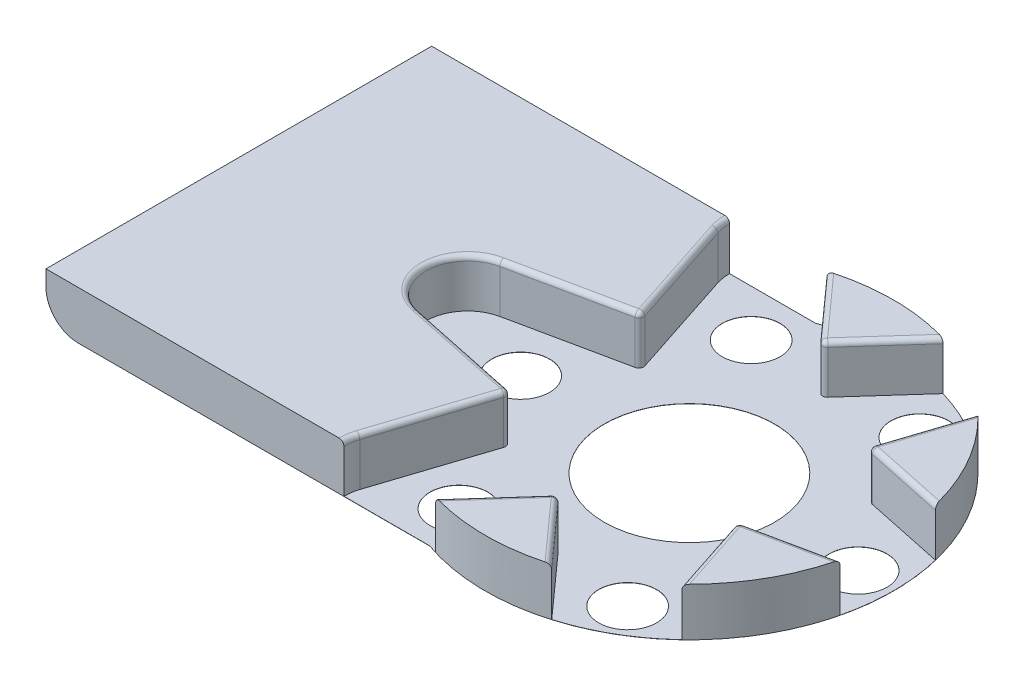
SolidWorks part; units mm, degrees
ref_plane "Alzado" through (0, 0, 0) normal (0, 0, 1) x (1, 0, 0)
ref_plane "Planta" through (0, 0, 0) normal (0, 1, 0) x (1, 0, 0)
ref_plane "Vista lateral" through (0, 0, 0) normal (1, 0, 0) x (0, 0, -1)
sketch "Croquis1" plane through (0, 0, 0) normal (0, 1, 0) x (1, 0, 0)
  line L0 (-28.04, 12) -> (-4.1581, 12)
  line L1 (-28.04, -12) -> (-4.1581, -12)
  line L2 (-28.04, 12) -> (-28.04, -12)
  line L3 (-28.04, 0) -> (0, 0) construction
  arc A0 (-4.1581, -12) -> (-4.1581, 12) centre (0, 0) ccw
  circle A1 centre (0, 0) radius 5.3
  dimension "D1" = 25.4
  dimension "D3" = 10.6
  dimension "D2" = 24
  dimension "D4" = 28.04
extrude "Saliente-Extruir1" add sketch "Croquis1" along normal blind 3
sketch "Croquis2" plane through (0, 3, 0) normal (0, 1, 0) x (1, 0, 0)
  line L0 (0, 0) -> (-13.8, 0) construction
  line L1 (-14.3352, -2.5443) -> (-7.0581, -4.075)
  line L2 (-14.3352, 2.5443) -> (-7.0581, 4.075)
  line L3 (-4.9641, 13.6868) -> (0, 8.15)
  line L4 (-9.371, 11.1425) -> (-7.0581, 4.075)
  line L5 (9.371, 11.1425) -> (7.0581, 4.075)
  line L6 (4.9641, 13.6868) -> (0, 8.15)
  line L7 (14.3352, -2.5443) -> (7.0581, -4.075)
  line L8 (14.3352, 2.5443) -> (7.0581, 4.075)
  line L9 (4.9641, -13.6868) -> (0, -8.15)
  line L10 (9.371, -11.1425) -> (7.0581, -4.075)
  line L11 (-9.371, -11.1425) -> (-7.0581, -4.075)
  line L12 (-4.9641, -13.6868) -> (0, -8.15)
  circle A0 centre (0, 0) radius 13.8 construction
  circle A1 centre (0, 0) radius 8.15 construction
  arc A2 (-14.3352, 2.5443) -> (-14.3352, -2.5443) centre (-13.8, 0) ccw
  arc A3 (-4.9641, 13.6868) -> (-9.371, 11.1425) centre (-6.9, 11.9512) ccw
  arc A4 (9.371, 11.1425) -> (4.9641, 13.6868) centre (6.9, 11.9512) ccw
  arc A5 (14.3352, -2.5443) -> (14.3352, 2.5443) centre (13.8, 0) ccw
  arc A6 (4.9641, -13.6868) -> (9.371, -11.1425) centre (6.9, -11.9512) ccw
  arc A7 (-9.371, -11.1425) -> (-4.9641, -13.6868) centre (-6.9, -11.9512) ccw
  circle A8 centre (0, 0) radius 16.4 construction
  point P43 (0, 0)
  dimension "D1" = 16.3
  dimension "D2" = 5.2
  dimension "D4" = 32.8
  dimension "D3" = 6
extrude "Cortar-Extruir2" cut sketch "Croquis2" against normal offset from surface (2.99 mm away) 0.01 up to face at (-11.8845, 0, 0)
fillet "Redondeo1" radius 2 1 edges at (-28.04, 0, 0)
fillet "Redondeo2" radius 0.3 21 edges at (-10.6966, 3, 3.3097) (7.0581, 1.505, 4.075) (-7.0581, 1.505, -4.075) (-7.0581, 1.505, 4.075) (0, 1.505, 8.15) (0, 1.505, -8.15) (7.0581, 1.505, -4.075) (9.7039, 3, 3.5185) (7.8991, 3, 6.6446) (1.8049, 3, 10.1631) (9.7039, 3, -3.5185) (7.8991, 3, -6.6446) (1.8049, 3, -10.1631) (-1.8049, 3, -10.1631) (-9.4713, 3, -11.5658) (-9.4713, 3, 11.5658) (-8.2146, 3, 7.6087) (-1.8049, 3, 10.1631) (-8.2146, 3, -7.6087) (-10.6966, 3, -3.3097) (-16.4, 3, 0)
sketch "Croquis3" plane through (0, 0, 0) normal (0, -1, 0) x (1, 0, 0)
  circle A0 centre (0, 0) radius 10.5 construction
  circle A1 centre (10.5, 0) radius 1.8
  dimension "D1" = 21
  dimension "D2" = 3.6
extrude "Cortar-Extruir3" cut sketch "Croquis3" against normal blind 10
pattern_circular "MatrizC1" count 6 over 360 about axis through (0, 0, 0) along (0, 1, 0) of "Cortar-Extruir3"
